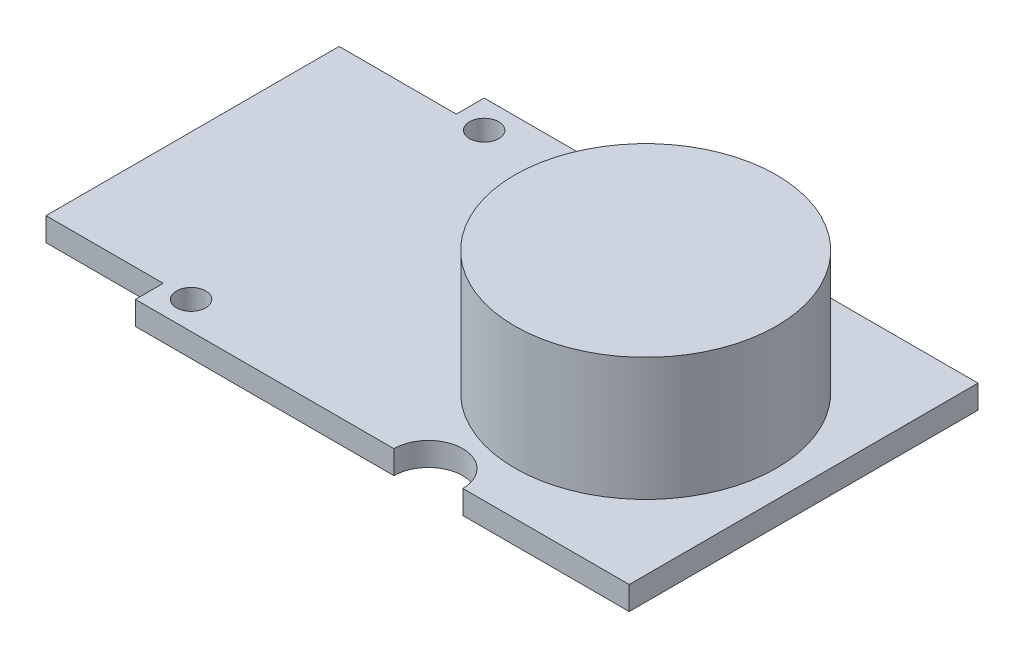
SolidWorks part; units mm, degrees
ref_plane "Front Plane" through (0, 0, 0) normal (0, 0, 1) x (1, 0, 0)
ref_plane "Top Plane" through (0, 0, 0) normal (0, 1, 0) x (1, 0, 0)
ref_plane "Right Plane" through (0, 0, 0) normal (1, 0, 0) x (0, 0, -1)
sketch "Sketch1" plane through (0, 0, 0) normal (0, 1, 0) x (1, 0, 0)
  line L0 (0, 0) -> (-30.9202, 0) construction
  line L1 (-30.9202, 11.9) -> (10.7798, 11.9)
  line L2 (-30.9202, 11.9) -> (-30.9202, -11.9)
  line L3 (-30.9202, -11.9) -> (10.7798, -11.9)
  line L4 (10.7798, 11.9) -> (10.7798, -11.9)
  circle A0 centre (0, 0) radius 8.7798
  circle A1 centre (-2.9301, 11.9) radius 2.35
  circle A2 centre (-2.9301, -11.9) radius 2.35
  circle A3 centre (-21.0202, 10) radius 1
  circle A4 centre (-21.0202, -10) radius 1
  point P8 (10.7798, 0)
  point P9 (8.7798, 0)
  dimension "D4" = 4.7
  dimension "D5" = 2
  dimension "D6" = 20
  dimension "D1" = 41.7
  dimension "D2" = 23.8
  dimension "D3" = 2
  dimension "D7" = 9.9
extrude "Boss-Extrude1" add sketch "Sketch1" along normal blind 1.6
sketch "Sketch2" plane through (0, 1.6, 0) normal (0, 1, 0) x (1, 0, 0)
  circle A0 centre (0, 0) radius 8.9314
extrude "Boss-Extrude2" add sketch "Sketch2" along normal blind 8.4
sketch "Sketch3" plane through (0, 1.6, 0) normal (0, 1, 0) x (1, 0, 0)
  line L0 (-21.0202, 10) -> (-20.0202, 10) construction
  line L1 (-30.9202, 11.9) -> (-22.9202, 11.9)
  line L2 (-30.9202, 11.9) -> (-30.9202, 10)
  line L3 (-30.9202, 10) -> (-22.9202, 10)
  line L4 (-22.9202, 11.9) -> (-22.9202, 10)
  line L5 (-30.9202, -11.9) -> (-22.9202, -11.9)
  line L6 (-30.9202, -11.9) -> (-30.9202, -10)
  line L7 (-30.9202, -10) -> (-22.9202, -10)
  line L8 (-22.9202, -11.9) -> (-22.9202, -10)
  circle A0 centre (-21.0202, 10) radius 1 construction
  point P15 (-23.7274, 10)
  dimension "D1" = 8
extrude "Cut-Extrude1" cut sketch "Sketch3" against normal through all both and the other way through all
